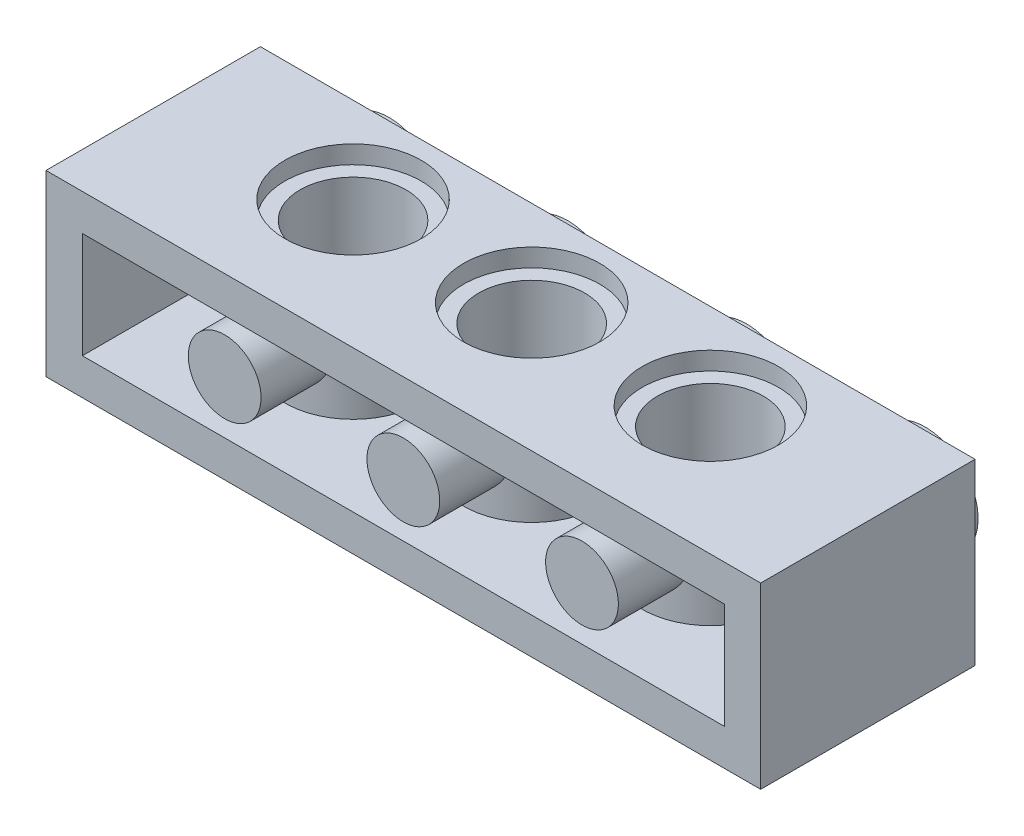
SolidWorks part; units mm, degrees
material "Custom Plastic"
ref_plane "Front Plane" through (0, 0, 0) normal (0, 0, 1) x (1, 0, 0)
ref_plane "Top Plane" through (0, 0, 0) normal (0, 1, 0) x (1, 0, 0)
ref_plane "Right Plane" through (0, 0, 0) normal (1, 0, 0) x (0, 0, -1)
ref_plane "Plane1" through (0, 4.0325, 0) normal (0, 1, 0) x (-1, 0, 0)
sketch "Sketch1" plane through (0, 4.0325, 0) normal (0, 1, 0) x (-1, 0, 0)
  line L0 (-16.13, 4.839) -> (-16.13, -4.839)
  line L1 (-16.13, -4.839) -> (16.13, -4.839)
  line L2 (16.13, -4.839) -> (16.13, 4.839)
  line L3 (16.13, 4.839) -> (-16.13, 4.839)
extrude "Boss-Extrude1" add sketch "Sketch1" against normal blind 8.065
sketch "Sketch2" plane through (0, 0, 4.839) normal (0, 0, 1) x (1, 0, 0)
  line L0 (-14.4875, -2.39) -> (14.4875, -2.39)
  line L1 (14.4875, -2.39) -> (14.4875, 2.39)
  line L2 (14.4875, 2.39) -> (-14.4875, 2.39)
  line L3 (-14.4875, 2.39) -> (-14.4875, -2.39)
extrude "Cut-Extrude1" cut sketch "Sketch2" against normal blind 8.0355
sketch "Sketch3" plane through (0, 2.39, 0) normal (0, -1, 0) x (1, 0, 0)
  line L0 (10.1711, -3.1965) -> (5.9589, -3.1965)
  arc A0 (5.9589, -3.1965) -> (10.1711, -3.1965) centre (8.065, -0.956) cw
extrude "Boss-Extrude2" add sketch "Sketch3" along normal blind 4.78
sketch "Sketch4" plane through (0, 2.39, 0) normal (0, -1, 0) x (1, 0, 0)
  line L0 (2.1061, -3.1965) -> (-2.1061, -3.1965)
  arc A0 (-2.1061, -3.1965) -> (2.1061, -3.1965) centre (0, -0.956) cw
extrude "Boss-Extrude3" add sketch "Sketch4" along normal blind 4.78
sketch "Sketch5" plane through (0, 2.39, 0) normal (0, -1, 0) x (1, 0, 0)
  line L0 (-5.9589, -3.1965) -> (-10.1711, -3.1965)
  arc A0 (-10.1711, -3.1965) -> (-5.9589, -3.1965) centre (-8.065, -0.956) cw
extrude "Boss-Extrude4" add sketch "Sketch5" along normal blind 4.78
ref_plane "Plane2" through (0, 0, 0) normal (0, -1, 0) x (1, 0, 0)
sketch "Sketch6" plane through (0, 0, 0) normal (0, -1, 0) x (1, 0, 0)
  line L0 (14.4875, -4.839) -> (12.0975, -4.839)
  line L1 (12.0975, -4.839) -> (12.0975, -6.619)
  line L2 (12.0975, -6.619) -> (14.4875, -6.619)
  line L3 (14.4875, -6.619) -> (14.4875, -4.839)
  line L4 (12.0975, -4.839) -> (12.0975, -6.619) construction
revolve "Revolve1" add sketch "Sketch6" angle 360 about L4
sketch "Sketch7" plane through (0, 0, 0) normal (0, -1, 0) x (1, 0, 0)
  line L0 (6.4225, -4.839) -> (4.0325, -4.839)
  line L1 (4.0325, -4.839) -> (4.0325, -6.619)
  line L2 (4.0325, -6.619) -> (6.4225, -6.619)
  line L3 (6.4225, -6.619) -> (6.4225, -4.839)
  line L4 (4.0325, -4.839) -> (4.0325, -6.619) construction
revolve "Revolve2" add sketch "Sketch7" angle 360 about L4
sketch "Sketch8" plane through (0, 0, 0) normal (0, -1, 0) x (1, 0, 0)
  line L0 (-1.6425, -4.839) -> (-4.0325, -4.839)
  line L1 (-4.0325, -4.839) -> (-4.0325, -6.619)
  line L2 (-4.0325, -6.619) -> (-1.6425, -6.619)
  line L3 (-1.6425, -6.619) -> (-1.6425, -4.839)
  line L4 (-4.0325, -4.839) -> (-4.0325, -6.619) construction
revolve "Revolve3" add sketch "Sketch8" angle 360 about L4
sketch "Sketch9" plane through (0, 0, 0) normal (0, -1, 0) x (1, 0, 0)
  line L0 (-9.7075, -4.839) -> (-12.0975, -4.839)
  line L1 (-12.0975, -4.839) -> (-12.0975, -6.619)
  line L2 (-12.0975, -6.619) -> (-9.7075, -6.619)
  line L3 (-9.7075, -6.619) -> (-9.7075, -4.839)
  line L4 (-12.0975, -4.839) -> (-12.0975, -6.619) construction
revolve "Revolve4" add sketch "Sketch9" angle 360 about L4
ref_plane "Plane3" through (0, 0, -0.956) normal (0, 0, -1) x (-1, 0, 0)
sketch "Sketch10" plane through (0, 0, -0.956) normal (0, 0, -1) x (-1, 0, 0)
  line L0 (-11.14, -4.0325) -> (-8.065, -4.0325)
  line L1 (-8.065, -4.0325) -> (-8.065, 4.0325)
  line L2 (-8.065, 4.0325) -> (-11.14, 4.0325)
  line L3 (-11.14, 4.0325) -> (-11.14, 3.2175)
  line L4 (-11.14, 3.2175) -> (-10.455, 3.2175)
  line L5 (-10.455, 3.2175) -> (-10.455, -3.2175)
  line L6 (-10.455, -3.2175) -> (-11.14, -3.2175)
  line L7 (-11.14, -3.2175) -> (-11.14, -4.0325)
  line L8 (-8.065, -4.0325) -> (-8.065, 4.0325) construction
revolve "Cut-Revolve1" cut sketch "Sketch10" angle 360 about L8
sketch "Sketch11" plane through (0, 0, -0.956) normal (0, 0, -1) x (-1, 0, 0)
  line L0 (-3.075, -4.0325) -> (0, -4.0325)
  line L1 (0, -4.0325) -> (0, 4.0325)
  line L2 (0, 4.0325) -> (-3.075, 4.0325)
  line L3 (-3.075, 4.0325) -> (-3.075, 3.2175)
  line L4 (-3.075, 3.2175) -> (-2.39, 3.2175)
  line L5 (-2.39, 3.2175) -> (-2.39, -3.2175)
  line L6 (-2.39, -3.2175) -> (-3.075, -3.2175)
  line L7 (-3.075, -3.2175) -> (-3.075, -4.0325)
  line L8 (0, -4.0325) -> (0, 4.0325) construction
revolve "Cut-Revolve2" cut sketch "Sketch11" angle 360 about L8
sketch "Sketch12" plane through (0, 0, -0.956) normal (0, 0, -1) x (-1, 0, 0)
  line L0 (4.99, -4.0325) -> (8.065, -4.0325)
  line L1 (8.065, -4.0325) -> (8.065, 4.0325)
  line L2 (8.065, 4.0325) -> (4.99, 4.0325)
  line L3 (4.99, 4.0325) -> (4.99, 3.2175)
  line L4 (4.99, 3.2175) -> (5.675, 3.2175)
  line L5 (5.675, 3.2175) -> (5.675, -3.2175)
  line L6 (5.675, -3.2175) -> (4.99, -3.2175)
  line L7 (4.99, -3.2175) -> (4.99, -4.0325)
  line L8 (8.065, -4.0325) -> (8.065, 4.0325) construction
revolve "Cut-Revolve3" cut sketch "Sketch12" angle 360 about L8
ref_plane "Plane4" through (-8.065, 0, 0) normal (1, 0, 0) x (0, 0, -1)
sketch "Sketch13" plane through (-8.065, 0, 0) normal (1, 0, 0) x (0, 0, -1)
  line L0 (-4.839, 1.6425) -> (-4.839, 0)
  line L1 (-4.839, 0) -> (-1.6436, 0)
  line L2 (-1.6436, 0) -> (-1.6436, 1.6425)
  line L3 (-1.6436, 1.6425) -> (-4.839, 1.6425)
  line L4 (-4.839, 0) -> (-1.6436, 0) construction
revolve "Revolve5" add sketch "Sketch13" angle 360 about L4
sketch "Sketch14" plane through (0, 0, 0) normal (1, 0, 0) x (0, 0, -1)
  line L0 (-4.839, 1.6425) -> (-4.839, 0)
  line L1 (-4.839, 0) -> (-1.6436, 0)
  line L2 (-1.6436, 0) -> (-1.6436, 1.6425)
  line L3 (-1.6436, 1.6425) -> (-4.839, 1.6425)
  line L4 (-4.839, 0) -> (-1.6436, 0) construction
revolve "Revolve6" add sketch "Sketch14" angle 360 about L4
ref_plane "Plane5" through (8.065, 0, 0) normal (1, 0, 0) x (0, 0, -1)
sketch "Sketch15" plane through (8.065, 0, 0) normal (1, 0, 0) x (0, 0, -1)
  line L0 (-4.839, 1.6425) -> (-4.839, 0)
  line L1 (-4.839, 0) -> (-1.6436, 0)
  line L2 (-1.6436, 0) -> (-1.6436, 1.6425)
  line L3 (-1.6436, 1.6425) -> (-4.839, 1.6425)
  line L4 (-4.839, 0) -> (-1.6436, 0) construction
revolve "Revolve7" add sketch "Sketch15" angle 360 about L4
hole_wizard "M3 Clearance Hole1" positions "Sketch17" profile "Sketch16" hole size "M3" standard "Ansi Metric"
sketch "Sketch17" plane through (0, 0, -6.619) normal (0, 0, -1) x (-1, 0, 0)
  point P0 (12.0975, 0)
  point P1 (4.0325, 0)
  point P2 (-4.0325, 0)
  point P3 (-12.0975, 0)
sketch "Sketch16" plane through (-12.0975, 0, -6.619) normal (1, 0, 0) x (0, 1, 0)
  line L0 (0, 0) -> (0, 1.78)
  line L1 (0, 1.78) -> (1.6425, 1.78)
  line L2 (1.6425, 1.78) -> (1.6425, 0)
  line L5 (1.6425, 0) -> (0, 0)
  line L10 (0, 1.78) -> (-1.6425, 1.78) construction
  line L11 (0, -6.35) -> (0, 107.95) construction
  dimension "Hole Dia." = 3.285
  dimension "Hole Depth" = 1.78
  dimension "Drill Angle" = 180
